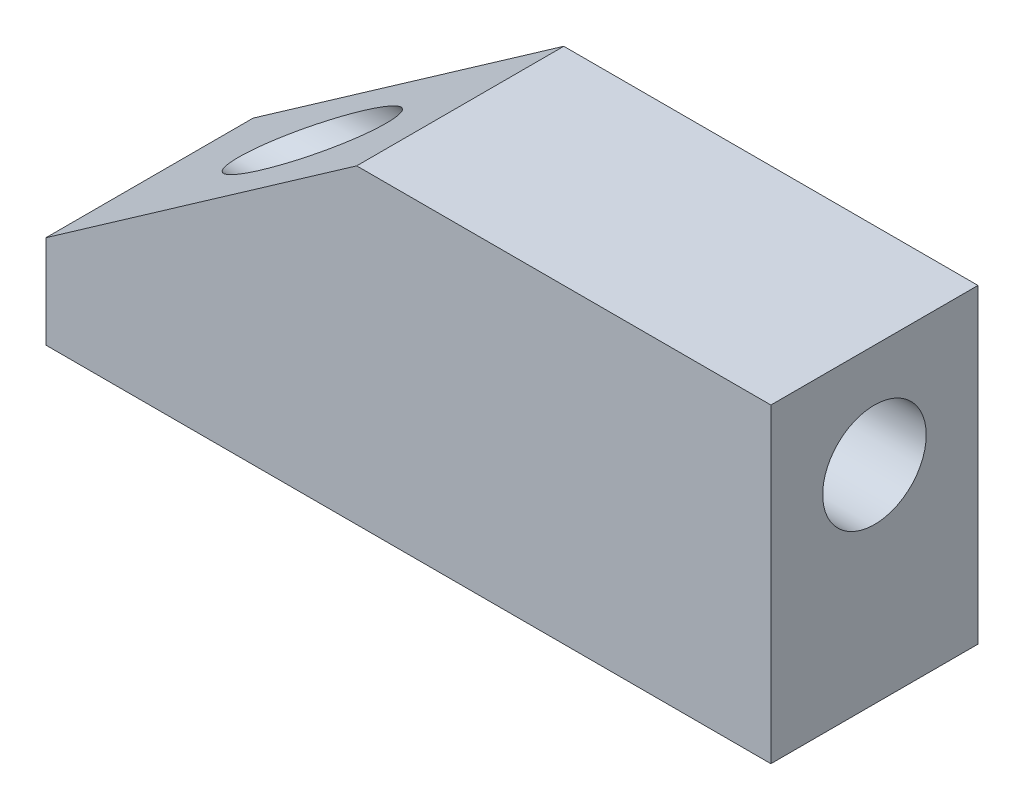
SolidWorks part; units mm, degrees
material "ABS"
ref_plane "前视基准面" through (0, 0, 0) normal (0, 0, 1) x (1, 0, 0)
ref_plane "上视基准面" through (0, 0, 0) normal (0, 1, 0) x (1, 0, 0)
ref_plane "右视基准面" through (0, 0, 0) normal (1, 0, 0) x (0, 0, -1)
other "Configuration Table"
sketch "草图1" plane through (0, 0, 0) normal (0, 0, 1) x (1, 0, 0)
  line L0 (48.4874, 20.4279) -> (48.4874, 24.9248)
  line L1 (48.4874, 24.9248) -> (63.4874, 35.4279)
  line L2 (63.4874, 35.4279) -> (83.4874, 35.4279)
  line L3 (83.4874, 35.4279) -> (83.4874, 20.4279)
  line L4 (83.4874, 20.4279) -> (48.4874, 20.4279)
  dimension "D1" = 15
  dimension "D2" = 35
  dimension "D3" = 20
  dimension "D4" = 55
extrude "凸台-拉伸1" add sketch "草图1" along normal blind 10
sketch "草图2" plane through (83.4874, 0, 0) normal (1, 0, 0) x (0, 0, -1)
  line L0 (-5, 20.4279) -> (-5, 35.4279) construction
  line L1 (-10, 20.4279) -> (0, 20.4279) construction
  line L2 (-10, 35.4279) -> (0, 35.4279) construction
  circle A0 centre (-5, 30.4279) radius 2.5
  dimension "D1" = 10
  dimension "D2" = 5
extrude "切除-拉伸1" cut sketch "草图2" against normal through all
